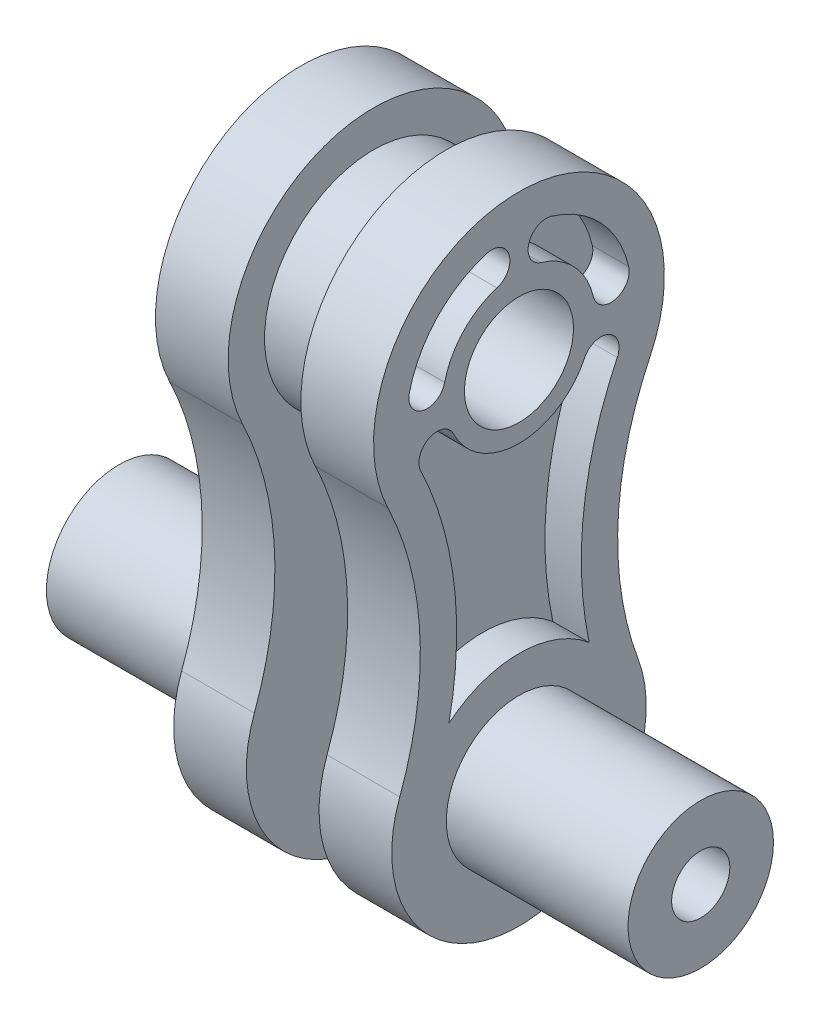
SolidWorks part; units mm, degrees
material "AISI 304"
ref_plane "Front Plane" through (0, 0, 0) normal (0, 0, 1) x (1, 0, 0)
ref_plane "Top Plane" through (0, 0, 0) normal (0, 1, 0) x (1, 0, 0)
ref_plane "Right Plane" through (0, 0, 0) normal (1, 0, 0) x (0, 0, -1)
sketch "Sketch1" plane through (0, 0, 0) normal (1, 0, 0) x (0, 0, -1)
  circle A0 centre (0, 0) radius 30
  dimension "D1" = 60
extrude "Boss-Extrude1" add sketch "Sketch1" along normal mid plane 20
sketch "Sketch2" plane through (10, 0, 0) normal (1, 0, 0) x (0, 0, -1)
  line L0 (0, -154.0905) -> (0, 67.6699) construction
  arc A0 (36.0432, -17.3462) -> (-36.0432, -17.3462) centre (0, 0) ccw
  arc A1 (-32.7993, -87.785) -> (32.7993, -87.785) centre (0, -100) ccw
  arc A2 (-32.7993, -87.785) -> (-36.0432, -17.3462) centre (-117.1403, -56.375) ccw
  arc A3 (32.7993, -87.785) -> (36.0432, -17.3462) centre (117.1403, -56.375) cw
  dimension "D1" = 90
  dimension "D2" = 40
  dimension "D3" = 35
  dimension "D4" = 100
extrude "Boss-Extrude2" add sketch "Sketch2" along normal blind 20
sketch "Sketch3" plane through (30, 0, 0) normal (1, 0, 0) x (0, 0, -1)
  circle A0 centre (0, -100) radius 20
  dimension "D1" = 40
extrude "Boss-Extrude3" add sketch "Sketch3" along normal blind 50
sketch "Sketch4" plane through (30, 0, 0) normal (1, 0, 0) x (0, 0, -1)
  line L1 (0, -32.9207) -> (0, 48.4027) construction
  arc A1 (7.5, 24.8948) -> (25.3095, 5.9522) centre (0, 0) cw construction
  arc A2 (30.1767, 7.0969) -> (8.9423, 29.6822) centre (0, 0) ccw
  arc A3 (20.4423, 4.8075) -> (6.0577, 20.1073) centre (0, 0) ccw
  arc A4 (20.4423, 4.8075) -> (30.1767, 7.0969) centre (25.3095, 5.9522) ccw
  arc A5 (8.9423, 29.6822) -> (6.0577, 20.1073) centre (7.5, 24.8948) ccw
  arc A6 (-7.5, 24.8948) -> (-25.3095, 5.9522) centre (0, 0) ccw construction
  arc A7 (-30.1767, 7.0969) -> (-8.9423, 29.6822) centre (0, 0) cw
  arc A8 (-20.4423, 4.8075) -> (-6.0577, 20.1073) centre (0, 0) cw
  arc A9 (-20.4423, 4.8075) -> (-30.1767, 7.0969) centre (-25.3095, 5.9522) cw
  arc A10 (-8.9423, 29.6822) -> (-6.0577, 20.1073) centre (-7.5, 24.8948) cw
  circle A84 centre (0, -100) radius 30
  arc A85 (27.0324, -13.0096) -> (23.4281, -91.275) centre (117.1403, -56.375) ccw
  arc A86 (27.0324, -13.0096) -> (-27.0324, -13.0096) centre (0, 0) ccw
  arc A87 (-23.4281, -91.275) -> (-27.0324, -13.0096) centre (-117.1403, -56.375) ccw
  arc A88 (27.0324, -13.0096) -> (19.2967, -77.0296) centre (117.1403, -56.375) ccw
  arc A90 (-19.2967, -77.0296) -> (-27.0324, -13.0096) centre (-117.1403, -56.375) ccw
  arc A91 (19.2967, -77.0296) -> (-19.2967, -77.0296) centre (0, -100) ccw
  arc A92 (-18.0216, -8.6731) -> (-27.0324, -13.0096) centre (-22.527, -10.8413) ccw
  arc A93 (27.0324, -13.0096) -> (18.0216, -8.6731) centre (22.527, -10.8413) ccw
  arc A101 (-18.0216, -8.6731) -> (18.0216, -8.6731) centre (0, 0) ccw
  point P2 (18.9426, 17.8095)
  point P27 (-18.9426, 17.8095)
  dimension "D3" = 26
  dimension "D4" = 10
  dimension "D5" = 5
  dimension "D6" = 60
  dimension "D7" = 7.5
  dimension "D1" = 10
  dimension "D2" = 10
extrude "Cut-Extrude1" cut sketch "Sketch4" against normal blind 10
sketch "Sketch5" plane through (30, 0, 0) normal (1, 0, 0) x (0, 0, -1)
  circle A0 centre (0, 0) radius 15
  dimension "D1" = 30
extrude "Cut-Extrude2" cut sketch "Sketch5" against normal through all
sketch "Sketch6" plane through (80, 0, 0) normal (1, 0, 0) x (0, 0, -1)
  circle A0 centre (0, -100) radius 8
  dimension "D1" = 16
extrude "Cut-Extrude3" cut sketch "Sketch6" against normal through all
mirror "Mirror1" about plane through (0, 0, 0) normal (1, 0, 0) of "Cut-Extrude3", "Cut-Extrude2", "Cut-Extrude1", "Boss-Extrude3", "Boss-Extrude2"
